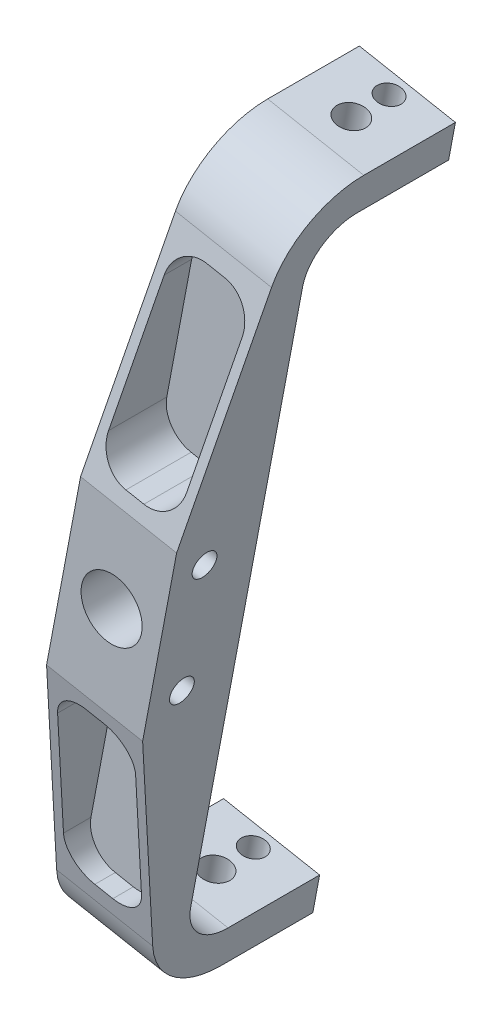
SolidWorks part; units mm, degrees
other "Markup1"
sketch "Sketch6" plane through (39.3536, 123.4271, -45) normal (0.998, 0.0328, -0.0532) x (-0.0595, 0.2351, -0.9701)
other "Markup2"
sketch "Sketch7" plane through (39.3536, 123.4271, -45) normal (0.9999, 0.0057, -0.0131) x (0.0031, -0.9818, -0.1901)
other "Markup4"
sketch "Sketch9" plane through (-39.3536, 123.4271, 27) normal (-0.9915, 0.1233, 0.0413) x (-0.1205, -0.9906, 0.0646)
other "Markup5"
sketch "Sketch12" plane through (-39.3536, 123.4271, 28.5) normal (-0.7749, 0.0474, 0.6304) x (0.632, 0.0395, 0.7739)
material "6061-T6 (SS)"
ref_plane "Front Plane" through (0, 0, 0) normal (0, 0, 1) x (1, 0, 0)
ref_plane "Top Plane" through (0, 0, 0) normal (0, 1, 0) x (1, 0, 0)
ref_plane "Right Plane" through (0, 0, 0) normal (1, 0, 0) x (0, 0, -1)
sketch "Sketch1" plane through (0, 0, 0) normal (0, 0, 1) x (1, 0, 0)
  line L0 (23.3397, 123.7002) -> (23.3397, 145.9252) construction
  line L1 (0, 0) -> (0, -276.86) construction
  line L2 (0, -276.86) -> (-52.2377, -276.86) construction
  line L3 (23.3397, 123.7002) -> (-52.2377, -276.86) construction
  line L8 (-23.3397, -123.7002) -> (-27.4603, -145.5398) construction
  line L9 (-7.6171, -126.6667) -> (39.0622, 120.7336)
  line L14 (-39.0622, -120.7336) -> (7.6171, 126.6667)
  line L17 (23.3397, 123.7002) -> (27.4603, 145.5398) construction
  line L19 (-7.6171, -126.6667) -> (-39.0622, -120.7336)
  line L20 (-23.3397, -123.7002) -> (-25.4, -134.62) construction
  line L21 (7.6171, 126.6667) -> (39.0622, 120.7336)
  line L22 (23.3397, 123.7002) -> (-23.3397, -123.7002) construction
  circle A0 centre (0, 0) radius 276.86 construction
  circle A1 centre (0, 0) radius 10
  circle A2 centre (0, 0) radius 170.5 construction
  point P4 (25.4, 134.62)
  point P6 (0, 0)
  point P10 (0, -170.5)
  point P13 (-10.5081, -129.9032)
  point P17 (0, 0)
  point P18 (41.7595, 124.248)
  point P19 (-41.8145, -123.9803)
  point P20 (10.5081, 129.9032)
  point P25 (-25.4, -134.62)
  point P31 (0, 0)
  point P32 (-23.3397, -123.7002)
  dimension "D4" = 341
  dimension "D9" = 20
  dimension "D2" = 553.72
  dimension "D3" = 22.225
  dimension "D5" = 50.8
  dimension "D6" = 32
  dimension "D7" = 52.2377
  dimension "D8" = 251.7655
  dimension "D11" = 11.1125
  dimension "D12" = 269.24
extrude "Boss-Extrude1" add sketch "Sketch1" along normal blind 28.5
sketch "Sketch2" plane through (0, 0, 0) normal (0, 0, -1) x (-1, 0, 0)
  line L0 (-36.8373, 108.9417) -> (-5.3922, 114.8748)
  line L1 (5.3922, -114.8748) -> (36.8373, -108.9417)
  line L2 (-5.3922, 114.8748) -> (-7.6171, 126.6667)
  line L3 (5.3922, -114.8748) -> (7.6171, -126.6667)
  line L4 (-7.6171, 126.6667) -> (-39.0622, 120.7336)
  line L5 (-39.0622, 120.7336) -> (7.6171, -126.6667)
  line L6 (-7.6171, 126.6667) -> (-39.0622, 120.7336)
  line L7 (39.0622, -120.7336) -> (-7.6171, 126.6667)
  line L9 (-39.0622, 120.7336) -> (-36.8373, 108.9417)
  line L11 (39.0622, -120.7336) -> (36.8373, -108.9417)
  line L14 (7.6171, -126.6667) -> (39.0622, -120.7336)
  line L15 (7.6171, -126.6667) -> (39.0622, -120.7336)
  dimension "D2" = 12
  dimension "D1" = 0
extrude "Boss-Extrude2" add sketch "Sketch2" along normal blind 45
sketch "Sketch4" plane through (-1.6562, 128.4164, 0) normal (0.1854, 0.9827, 0) x (0.9827, -0.1854, 0)
  line L0 (25.4368, -28.5) -> (25.4368, 45) construction
  line L3 (9.4368, 45) -> (41.4368, 45) construction
  line L12 (9.4368, 26.6476) -> (41.4368, 26.6476) construction
  line L13 (9.4368, -28.5) -> (9.4368, 45) construction
  line L14 (41.4368, -28.5) -> (41.4368, 45) construction
  circle A0 centre (25.4368, 26.6476) radius 4.7625
  circle A1 centre (25.4368, 39) radius 3.9688
  point P6 (25.4368, 26.6476)
  dimension "D2" = 9.525
  dimension "D3" = 7.9375
  dimension "D1" = 18.3524
  dimension "D4" = 6
extrude "Cut-Extrude1" cut sketch "Sketch4" against normal through all
fillet "Fillet3" radius 15 2 edges at (21.1148, 111.9082, 0) (-21.1148, -111.9082, 0)
sketch "Sketch10" plane through (-16.0243, 1.3676, 0) normal (0.9827, -0.1854, 0) x (0, 0, -1)
  line L0 (-28.5, 31.6271) -> (-11.3167, 106.5459)
  line L1 (-28.5, 31.6271) -> (-46.9127, 31.4169)
  line L2 (-46.9127, 31.4169) -> (-44.7685, 140.1716)
  line L3 (-44.7685, 140.1716) -> (15, 127.5099)
  line L4 (0, 1.6271) -> (-52.8517, 1.6271) construction
  line L5 (-28.5, 127.5099) -> (45, 127.5099) construction
  line L6 (-28.5, -124.2556) -> (-28.5, 127.5099) construction
  line L7 (-44.7685, -136.9173) -> (15, -124.2556)
  line L8 (-46.9127, -28.1627) -> (-44.7685, -136.9173)
  line L9 (-28.5, -28.3729) -> (-46.9127, -28.1627)
  line L10 (-28.5, -28.3729) -> (-11.3167, -103.2916)
  line L11 (-28.5, 31.6271) -> (0, 31.6271) construction
  line L12 (0, -97.2556) -> (0, 100.5099) construction
  line L13 (-17.5, -18.3729) -> (-17.5, 21.6271) construction
  arc A0 (15, 115.5099) -> (0, 100.5099) centre (15, 100.5099) ccw construction
  arc A1 (15, 115.5099) -> (0, 100.5099) centre (15, 100.5099) ccw construction
  arc A2 (15, 127.5099) -> (-11.3167, 106.5459) centre (15, 100.5099) ccw
  arc A3 (15, -112.2556) -> (0, -97.2556) centre (15, -97.2556) cw construction
  arc A4 (15, -124.2556) -> (-11.3167, -103.2916) centre (15, -97.2556) cw
  circle A5 centre (-17.5, 21.6271) radius 4
  circle A6 centre (-17.5, -18.3729) radius 4
  point P6 (0, 0)
  point P14 (15, 127.5099)
  point P29 (15, -124.2556)
  point P37 (-17.5, 1.6271)
  dimension "D1" = 30
  dimension "D2" = 8
  dimension "D3" = 17.5
  dimension "D4" = 40
extrude "Cut-Extrude2" cut sketch "Sketch10" against normal through all both and the other way through all
sketch "Sketch11" plane through (0, 0, 28.5) normal (0, 0, 1) x (1, 0, 0)
  line L1 (0, 0) -> (75.6649, -14.2764) construction
  line L2 (35.1753, 100.1331) -> (21.2848, 26.5133) construction
  line L3 (35.1753, 100.1331) -> (21.2848, 26.5133) construction
  line L7 (3.5413, 34.9494) -> (9.4373, 33.8369)
  line L12 (-10.1604, 32.4464) -> (3.7302, 106.0662) construction
  line L13 (-10.1604, 32.4464) -> (3.7302, 106.0662) construction
  line L15 (21.118, 41.8095) -> (29.2542, 84.9314)
  line L26 (-4.4312, 46.6301) -> (3.705, 89.752)
  line L27 (2.6111, 100.1348) -> (34.0562, 94.2018) construction
  line L39 (15.3857, 97.7245) -> (21.2816, 96.6121)
  line L40 (-21.2848, -26.5133) -> (-35.1753, -100.1331) construction
  line L41 (-3.7302, -106.0662) -> (10.1604, -32.4464) construction
  line L42 (-21.2816, -96.6121) -> (-15.3857, -97.7245)
  line L43 (-21.118, -41.8095) -> (-29.2542, -84.9314)
  line L44 (4.4312, -46.6301) -> (-3.705, -89.752)
  line L45 (-9.4373, -33.8369) -> (-3.5413, -34.9494)
  arc A0 (9.4373, 33.8369) -> (21.118, 41.8095) centre (11.2913, 43.6636) ccw
  arc A1 (3.5413, 34.9494) -> (-4.4312, 46.6301) centre (5.3954, 44.776) cw
  arc A2 (15.3857, 97.7245) -> (3.705, 89.752) centre (13.5316, 87.8979) ccw
  arc A3 (29.2542, 84.9314) -> (21.2816, 96.6121) centre (19.4275, 86.7855) ccw
  arc A4 (-3.705, -89.752) -> (-15.3857, -97.7245) centre (-13.5316, -87.8979) cw
  arc A5 (-21.2816, -96.6121) -> (-29.2542, -84.9314) centre (-19.4275, -86.7855) cw
  arc A6 (-9.4373, -33.8369) -> (-21.118, -41.8095) centre (-11.2913, -43.6636) ccw
  arc A7 (-3.5413, -34.9494) -> (4.4312, -46.6301) centre (-5.3954, -44.776) cw
  point P12 (-3.4131, 31.3285)
  point P15 (10.5274, 99.16)
  point P16 (29.4323, 95.2747)
  point P17 (15.4917, 27.4432)
  point P18 (27.5728, 26.3797)
  point P19 (-17.6556, 26.3797)
  dimension "D4" = 10
  dimension "D2" = 6
  dimension "D1" = 35
  dimension "D3" = 6
extrude "Cut-Extrude4" cut sketch "Sketch11" against normal offset from surface (22.5 mm away) 6 up to face at (10, 0, 0)
